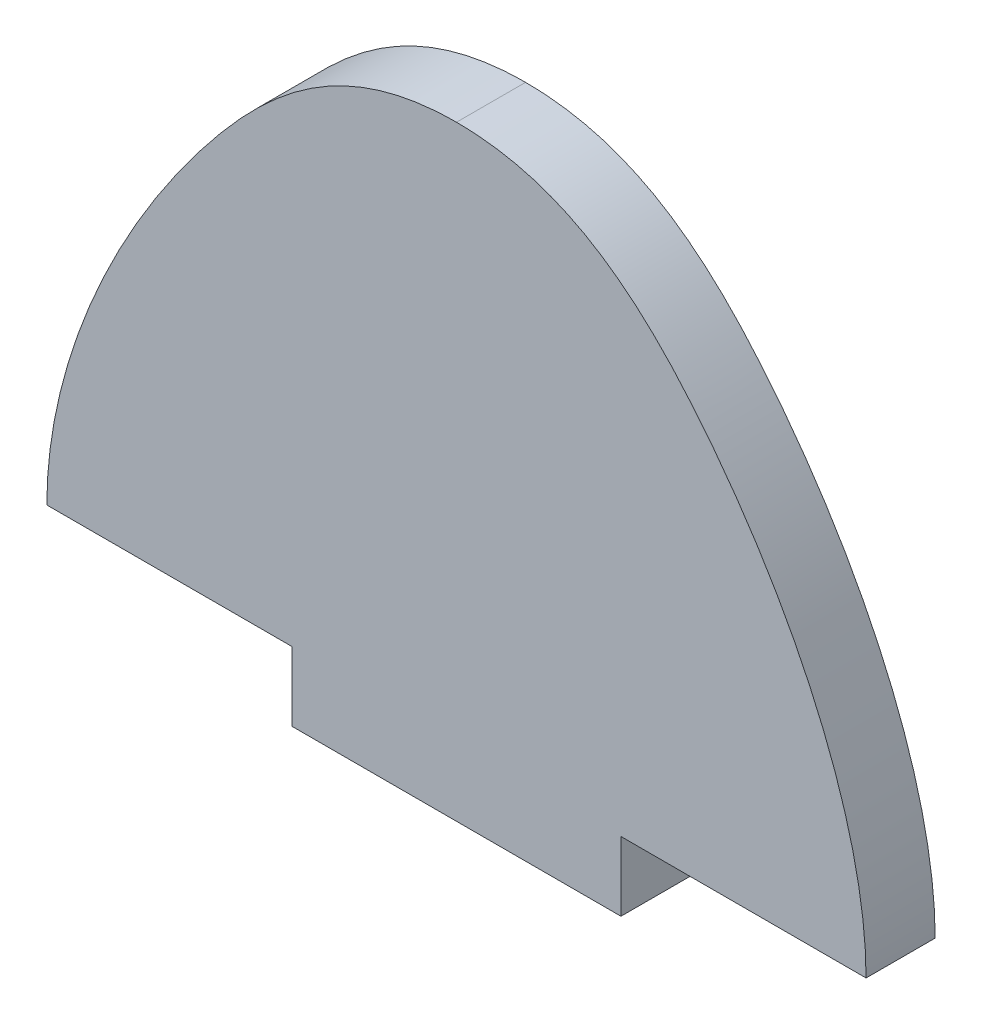
SolidWorks part; units mm, degrees
ref_plane "Front" through (0, 0, 0) normal (0, 0, 1) x (1, 0, 0)
ref_plane "Top" through (0, 0, 0) normal (0, 1, 0) x (1, 0, 0)
ref_plane "Right" through (0, 0, 0) normal (1, 0, 0) x (0, 0, -1)
sketch "Sketch1" plane through (0, 0, 0) normal (0, 0, 1) x (1, 0, 0)
  line L0 (52.578, 0) -> (35.814, 0) construction
  line L5 (35.814, 0) -> (16.764, 0) construction
  line L10 (16.764, 0) -> (0, 0) construction
  line L12 (52.578, 0) -> (35.814, 0)
  line L14 (13.589, 0) -> (38.989, 0)
  line L15 (13.589, 0) -> (13.589, -5.334)
  line L16 (13.589, -5.334) -> (38.989, -5.334)
  line L17 (35.814, 0) -> (16.764, 0)
  line L18 (38.989, 0) -> (38.989, -5.334)
  line L22 (16.764, 0) -> (0, 0)
  line L24 (26.289, 0) -> (26.289, 41.402) construction
  line L25 (0, 0) -> (-5.334, 0)
  line L30 (52.578, 0) -> (57.912, 0)
  spline S0 degree 3 poles (-5.334, 0) (-5.334, 10.0188) (3.6315, 29.2856) (17.6896, 41.402) (26.289, 41.402) knots 0 0 0 0 0.60439 1 1 1 1
  spline S1 degree 3 poles (57.912, 0) (57.912, 10.0188) (48.9465, 29.2856) (34.8884, 41.402) (26.289, 41.402) knots 0 0 0 0 0.60439 1 1 1 1
  point P8 (26.289, -5.334)
  dimension "D1" = 41.402
  dimension "D2" = 25.4
  dimension "D3" = 5.334
  dimension "D4" = 5.334
extrude "Boss-Extrude1" add sketch "Sketch1" along normal blind 5.334
